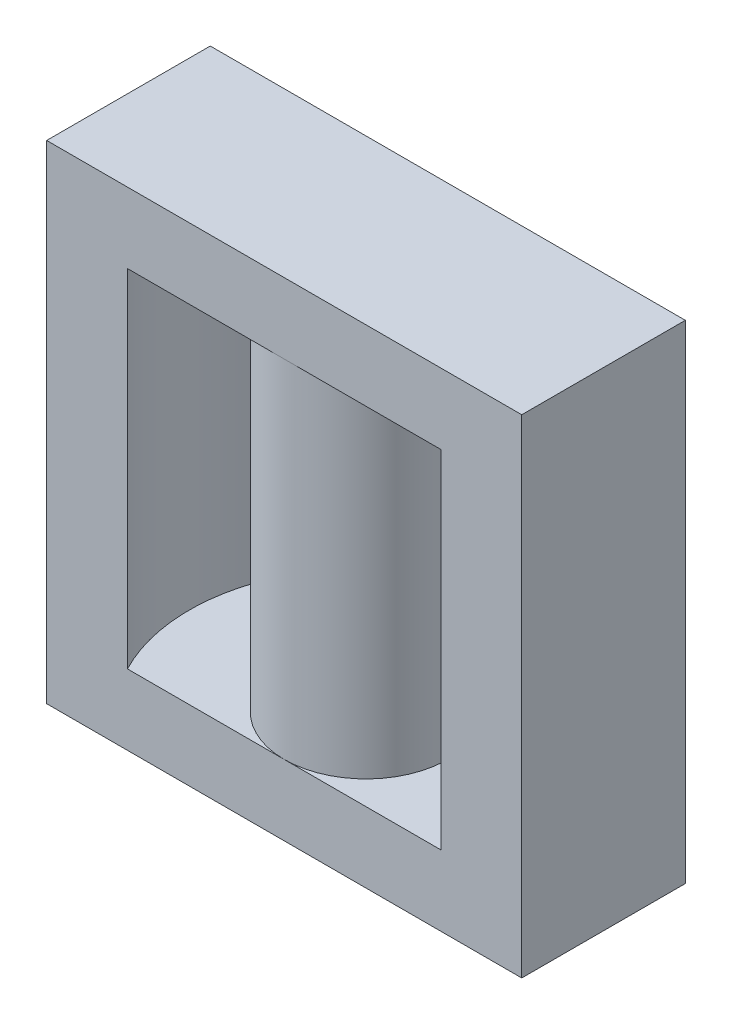
SolidWorks part; units mm, degrees
ref_plane "Front Plane" through (0, 0, 0) normal (0, 0, 1) x (1, 0, 0)
ref_plane "Top Plane" through (0, 0, 0) normal (0, 1, 0) x (1, 0, 0)
ref_plane "Right Plane" through (0, 0, 0) normal (1, 0, 0) x (0, 0, -1)
sketch "Sketch1" plane through (0, 0, 0) normal (0, 1, 0) x (1, 0, 0)
  line L1 (-24.25, 8.35) -> (24.25, 8.35)
  line L2 (-24.25, 8.35) -> (-24.25, -8.35)
  line L3 (-24.25, -8.35) -> (24.25, -8.35)
  line L4 (24.25, 8.35) -> (24.25, -8.35)
  circle A0 centre (0, 0) radius 8.35
  circle A1 centre (0, 0) radius 18.05
  dimension "D1" = 16.7
  dimension "D6" = 36.1
  dimension "D2" = 16.7
  dimension "D3" = 48.5
  dimension "D4" = 24.25
  dimension "D5" = 8.35
extrude "Boss-Extrude1" add sketch "Sketch1" along normal blind 49.8 contours A1 L1 L2 L3 | A0 | A1 L3 L4 L1
sketch "Sketch2" plane through (0, 49.8, 0) normal (0, 1, 0) x (1, 0, 0)
  line L1 (-24.25, 8.35) -> (24.25, 8.35)
  line L2 (-24.25, 8.35) -> (-24.25, -8.35)
  line L3 (-24.25, -8.35) -> (24.25, -8.35)
  line L4 (24.25, 8.35) -> (24.25, -8.35)
extrude "Boss-Extrude2" add sketch "Sketch2" against normal blind 7.2
sketch "Sketch3" plane through (0, 0, 0) normal (0, -1, 0) x (1, 0, 0)
  line L1 (-24.25, 8.35) -> (24.25, 8.35)
  line L2 (-24.25, 8.35) -> (-24.25, -8.35)
  line L3 (-24.25, -8.35) -> (24.25, -8.35)
  line L4 (24.25, 8.35) -> (24.25, -8.35)
extrude "Boss-Extrude3" add sketch "Sketch3" against normal blind 7.2
